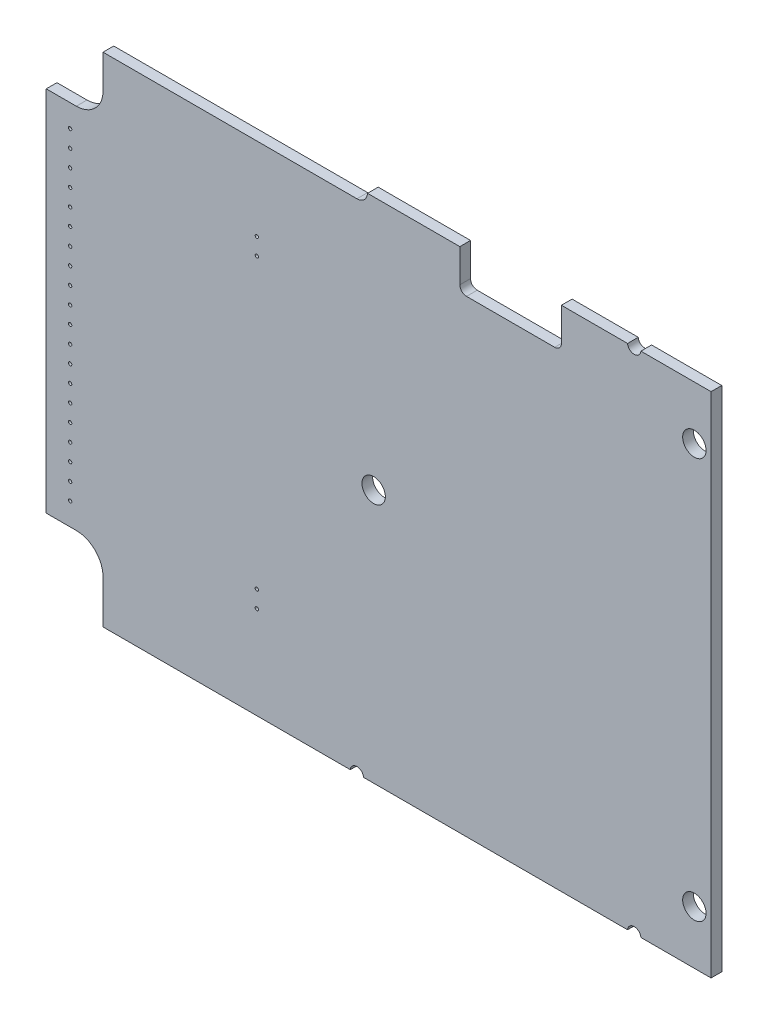
SolidWorks part; units mm, degrees
ref_plane "Płaszczyzna przednia" through (0, 0, 0) normal (0, 0, 1) x (1, 0, 0)
ref_plane "Płaszczyzna górna" through (0, 0, 0) normal (0, 1, 0) x (1, 0, 0)
ref_plane "Płaszczyzna prawa" through (0, 0, 0) normal (1, 0, 0) x (0, 0, -1)
sketch "Sketch1" plane through (0, 0, 0) normal (0, 0, 1) x (1, 0, 0)
  line L0 (293.2004, -11.8195) -> (291.7004, -11.8195) construction
  line L1 (291.7004, -11.8195) -> (291.7004, -12.7695) construction
  line L2 (308.8504, 57.7305) -> (322.0504, 57.7305)
  line L3 (293.2004, -12.7695) -> (293.2004, -11.8195) construction
  line L4 (334.7004, -11.8195) -> (333.2004, -11.8195) construction
  line L5 (333.2004, -11.8195) -> (333.2004, -12.7695) construction
  line L6 (333.2004, 63.6805) -> (333.2004, 63.2305) construction
  line L7 (334.7004, -12.7695) -> (334.7004, -11.8195) construction
  line L8 (376.2004, -11.8195) -> (374.7004, -11.8195) construction
  line L9 (374.7004, -11.8195) -> (374.7004, -12.7695) construction
  line L10 (333.2004, 63.2305) -> (333.2004, 63.1805) construction
  line L11 (376.2004, -12.7695) -> (376.2004, -11.8195) construction
  line L12 (393.4504, -5.0695) -> (393.4504, -6.5695) construction
  line L13 (393.4504, -6.5695) -> (394.4004, -6.5695) construction
  line L14 (333.2004, 63.6805) -> (332.9539, 63.6805) construction
  line L15 (394.4004, -5.0695) -> (393.4504, -5.0695) construction
  line L16 (393.4504, 57.9305) -> (393.4504, 56.4305) construction
  line L17 (393.4504, 56.4305) -> (394.4004, 56.4305) construction
  line L18 (333.2004, 63.6805) -> (323.0504, 63.6805) construction
  line L19 (394.4004, 57.9305) -> (393.4504, 57.9305) construction
  line L20 (333.2004, 63.1805) -> (334.7004, 63.1805) construction
  line L21 (334.7004, 63.1805) -> (334.7004, 64.1305) construction
  line L22 (333.2004, 64.425) -> (333.2004, 63.6805) construction
  line L23 (333.2004, 64.1305) -> (333.2004, 63.1805) construction
  line L24 (374.7004, 63.1805) -> (376.2004, 63.1805) construction
  line L25 (376.2004, 63.1805) -> (376.2004, 64.1305) construction
  line L26 (334.7004, 63.6805) -> (334.7004, 64.425) construction
  line L27 (374.7004, 64.1305) -> (374.7004, 63.1805) construction
  line L28 (291.7004, 63.1805) -> (293.2004, 63.1805) construction
  line L29 (293.2004, 63.1805) -> (293.2004, 64.1305) construction
  line L30 (291.4539, 63.6805) -> (254.4504, 63.6805) construction
  line L31 (291.7004, 64.1305) -> (291.7004, 63.1805) construction
  line L32 (376.2004, -13.3195) -> (390.9504, -13.3195) construction
  line L33 (394.9504, -9.3195) -> (394.9504, -6.5695) construction
  line L34 (394.9504, -5.0695) -> (394.9504, 56.4305) construction
  line L35 (394.9504, 57.9305) -> (394.9504, 60.6805) construction
  line L36 (390.9504, 64.6805) -> (376.2004, 64.6805) construction
  line L37 (374.7004, 64.6805) -> (334.7004, 64.6805) construction
  line L38 (307.8504, 64.6805) -> (307.8504, 65.8305) construction
  line L39 (323.0504, 64.6805) -> (323.0504, 65.8305) construction
  line L40 (333.2004, 64.6805) -> (323.0504, 64.6805) construction
  line L41 (307.8504, 64.6805) -> (293.2004, 64.6805) construction
  line L42 (291.7004, 64.6805) -> (246.9504, 64.6805) construction
  line L43 (246.9504, -8.4262) -> (246.9504, 59.7871) construction
  line L44 (334.7004, -13.3195) -> (374.7004, -13.3195) construction
  line L45 (293.2004, -13.3195) -> (333.2004, -13.3195) construction
  line L46 (246.9504, -13.3195) -> (291.7004, -13.3195) construction
  line L47 (293.2004, -11.8195) -> (291.7004, -11.8195) construction
  line L48 (291.7004, -11.8195) -> (291.7004, -13.3195) construction
  line L50 (293.2004, -13.3195) -> (293.2004, -11.8195) construction
  line L51 (334.7004, -11.8195) -> (333.2004, -11.8195) construction
  line L52 (333.2004, -11.8195) -> (333.2004, -13.3195) construction
  line L54 (334.7004, -13.3195) -> (334.7004, -11.8195) construction
  line L55 (376.2004, -11.8195) -> (374.7004, -11.8195) construction
  line L56 (374.7004, -11.8195) -> (374.7004, -13.3195) construction
  line L58 (376.2004, -13.3195) -> (376.2004, -13.0641) construction
  line L59 (393.4504, -5.0695) -> (393.4504, -6.5695) construction
  line L60 (393.4504, -6.5695) -> (394.9504, -6.5695) construction
  line L62 (394.9504, -5.0695) -> (393.4504, -5.0695) construction
  line L63 (393.4504, 57.9305) -> (393.4504, 56.4305) construction
  line L64 (393.4504, 56.4305) -> (394.6949, 56.4305) construction
  line L66 (394.9504, 57.9305) -> (393.4504, 57.9305) construction
  line L67 (333.2004, 63.1805) -> (334.7004, 63.1805) construction
  line L68 (334.7004, 63.1805) -> (334.7004, 63.6805) construction
  line L70 (333.2004, 64.6805) -> (333.2004, 64.425) construction
  line L71 (374.7004, 63.1805) -> (376.2004, 63.1805) construction
  line L72 (376.2004, 63.1805) -> (376.2004, 63.6805) construction
  line L74 (374.7004, 64.425) -> (374.7004, 63.1805) construction
  line L75 (291.7004, 63.1805) -> (293.2004, 63.1805) construction
  line L76 (293.2004, 63.1805) -> (293.2004, 64.6805) construction
  line L78 (291.7004, 64.425) -> (291.7004, 63.6805) construction
  line L79 (376.2004, -13.3195) -> (390.9504, -13.3195) construction
  line L80 (394.9504, -9.3195) -> (394.9504, -6.5695) construction
  line L81 (394.9504, -5.0695) -> (394.9504, 56.4305) construction
  line L82 (394.9504, 57.9305) -> (394.9504, 60.6805) construction
  line L83 (390.9504, 64.6805) -> (376.2004, 64.6805) construction
  line L84 (374.7004, 64.6805) -> (334.7004, 64.6805) construction
  line L85 (307.8504, 64.6805) -> (307.8504, 65.8305) construction
  line L86 (323.0504, 58.7305) -> (323.0504, 63.6805)
  line L87 (333.2004, 64.6805) -> (323.0504, 64.6805) construction
  line L88 (307.8504, 64.6805) -> (293.2004, 64.6805) construction
  line L89 (291.7004, 64.6805) -> (246.9504, 64.6805) construction
  line L90 (246.9504, -13.3195) -> (246.9504, -3.883) construction
  line L91 (334.7004, -13.3195) -> (374.7004, -13.3195) construction
  line L92 (293.2004, -13.3195) -> (333.2004, -13.3195) construction
  line L93 (246.9504, -13.3195) -> (291.7004, -13.3195) construction
  line L94 (247.9504, -12.3195) -> (247.9504, -8.942) construction
  line L95 (254.4504, -12.3195) -> (291.4539, -12.3195)
  line L96 (293.4469, -12.3195) -> (332.9539, -12.3195)
  line L97 (334.9469, -12.3195) -> (374.4539, -12.3195)
  line L98 (376.4469, -12.3195) -> (390.9504, -12.3195)
  line L99 (393.9504, -9.3195) -> (393.9504, -6.8161)
  line L100 (393.9504, -4.823) -> (393.9504, 56.4305)
  line L101 (393.9504, 58.177) -> (393.9504, 60.6805)
  line L102 (317.8504, 58.7305) -> (317.8504, 63.2305)
  line L103 (317.8504, 63.2305) -> (307.8504, 63.2305)
  line L104 (307.8504, 63.2305) -> (307.8504, 58.7305)
  line L105 (307.8504, 58.7305) -> (311.3504, 58.7305)
  line L106 (311.3504, 58.7305) -> (311.3504, 62.7305)
  line L107 (311.3504, 62.7305) -> (314.3504, 62.7305)
  line L108 (314.3504, 62.7305) -> (314.3504, 58.7305)
  line L109 (314.3504, 58.7305) -> (317.8504, 58.7305)
  line L112 (307.8504, 63.6805) -> (307.8504, 58.7305)
  line L113 (307.8504, 58.7305) -> (311.3504, 58.7305) construction
  line L114 (311.3504, 58.7305) -> (311.3504, 62.7305) construction
  line L115 (311.3504, 62.7305) -> (314.3504, 62.7305) construction
  line L116 (314.3504, 62.7305) -> (314.3504, 58.7305) construction
  line L117 (314.3504, 58.7305) -> (323.0504, 58.7305) construction
  line L118 (390.9504, 63.6805) -> (376.4469, 63.6805)
  line L119 (374.4539, 63.6805) -> (334.9469, 63.6805)
  line L120 (307.8504, 63.6805) -> (294.0313, 63.6805)
  line L121 (332.9539, 63.6805) -> (323.0504, 63.6805)
  line L122 (307.8504, 64.6805) -> (307.8504, 63.6805) construction
  line L123 (323.0504, 64.6805) -> (323.0504, 65.8305) construction
  line L124 (323.0504, 63.6805) -> (323.0504, 64.6805) construction
  line L125 (334.7004, 64.425) -> (334.7004, 64.6805) construction
  line L126 (334.9469, 63.6805) -> (334.7004, 63.6805) construction
  line L127 (374.7004, 63.6805) -> (334.7004, 63.6805) construction
  line L128 (291.7004, 63.6805) -> (291.4539, 63.6805) construction
  line L129 (291.7004, 63.6805) -> (247.9504, 63.6805) construction
  line L130 (291.7004, 64.6805) -> (291.7004, 64.425) construction
  line L131 (293.4469, 63.6805) -> (293.2004, 63.6805) construction
  line L132 (307.8504, 63.6805) -> (293.2004, 63.6805) construction
  line L133 (374.7004, 63.6805) -> (374.4539, 63.6805) construction
  line L134 (374.7004, 64.6805) -> (374.7004, 64.425) construction
  line L135 (376.2004, 63.6805) -> (376.2004, 64.425) construction
  line L136 (376.2004, 64.425) -> (376.2004, 64.6805) construction
  line L137 (376.4469, 63.6805) -> (376.2004, 63.6805) construction
  line L138 (390.9504, 63.6805) -> (376.2004, 63.6805) construction
  line L139 (394.6949, 56.4305) -> (394.9504, 56.4305) construction
  line L140 (393.9504, 57.9305) -> (393.9504, 58.177) construction
  line L141 (393.9504, 57.9305) -> (393.9504, 60.6805) construction
  line L142 (393.9504, -5.0695) -> (393.9504, -4.823) construction
  line L143 (393.9504, -5.0695) -> (393.9504, 56.4305) construction
  line L144 (393.9504, -6.8161) -> (393.9504, -6.5695) construction
  line L145 (393.9504, -9.3195) -> (393.9504, -6.5695) construction
  line L146 (376.2004, -13.0641) -> (376.2004, -12.3195) construction
  line L147 (376.2004, -12.3195) -> (376.2004, -11.8195) construction
  line L148 (376.2004, -12.3195) -> (376.4469, -12.3195) construction
  line L149 (376.2004, -12.3195) -> (390.9504, -12.3195) construction
  line L150 (293.2004, -12.3195) -> (293.4469, -12.3195) construction
  line L151 (332.9539, -12.3195) -> (333.2004, -12.3195) construction
  line L152 (293.2004, -12.3195) -> (333.2004, -12.3195) construction
  line L153 (334.7004, -12.3195) -> (334.9469, -12.3195) construction
  line L154 (334.7004, -12.3195) -> (374.7004, -12.3195) construction
  line L155 (254.4504, 57.1805) -> (254.4504, 62.1805)
  line L156 (291.4539, -12.3195) -> (291.7004, -12.3195) construction
  line L157 (247.9504, -12.3195) -> (291.7004, -12.3195) construction
  line L158 (250.4504, 53.1805) -> (245.9504, 53.1805)
  line L159 (254.4504, -5.8195) -> (254.4504, -12.3195)
  line L160 (250.4504, -1.8195) -> (245.9504, -1.8195)
  line L161 (247.9504, -1.8195) -> (247.9504, 53.1805) construction
  line L162 (247.9504, -4.1612) -> (247.9504, -2.697) construction
  line L163 (247.9504, -2.697) -> (247.9504, -1.8195) construction
  line L164 (247.9504, -12.3195) -> (247.9504, 63.6805) construction
  line L165 (247.9504, -8.942) -> (247.9504, -7.4778) construction
  line L166 (247.9504, -7.4778) -> (247.9504, -4.1612) construction
  line L167 (247.9504, -12.3195) -> (254.4504, -12.3195) construction
  line L168 (247.9504, 60.303) -> (247.9504, 63.6805) construction
  line L169 (254.4504, 63.6805) -> (247.9504, 63.6805) construction
  line L170 (247.9504, 58.8388) -> (247.9504, 60.303) construction
  line L171 (246.9504, 59.117) -> (246.9504, 64.6805) construction
  line L172 (246.9504, -13.3195) -> (246.9504, 64.6805) construction
  line L173 (246.9504, 55.244) -> (246.9504, 59.117) construction
  line L174 (247.9504, 55.5222) -> (247.9504, 58.8388) construction
  line L175 (246.9504, -3.883) -> (246.9504, 55.244) construction
  line L176 (247.9504, 54.058) -> (247.9504, 55.5222) construction
  line L177 (247.9504, 53.1805) -> (247.9504, 54.058) construction
  line L178 (249.5254, 49.8105) -> (277.4654, 49.8105) construction
  line L179 (249.5254, 49.8105) -> (249.5254, 47.2705) construction
  line L180 (374.4539, -12.3195) -> (374.7004, -12.3195) construction
  line L181 (245.4504, -8.8119) -> (245.4504, 59.8484) construction
  line L182 (245.4504, -8.8119) -> (245.4504, 59.8484) construction
  line L183 (245.9504, -1.8195) -> (245.9504, 53.1805)
  line L184 (245.9504, -8.8119) -> (245.9504, -1.8195) construction
  line L185 (245.9504, 53.1805) -> (245.9504, 59.8484) construction
  line L186 (245.9504, -8.8119) -> (245.9504, 59.8484) construction
  line L187 (292.4504, 62.7636) -> (254.4504, 62.7636) construction
  line L188 (254.4504, 62.7636) -> (254.4504, 63.6805) construction
  line L189 (291.7004, 63.6805) -> (291.7004, 63.2305) construction
  line L190 (291.7004, 63.2305) -> (291.7004, 63.1805) construction
  line L195 (292.4504, 62.1805) -> (254.4504, 62.1805)
  line L196 (294.0313, 63.6805) -> (293.4469, 63.6805) construction
  line L197 (254.4504, 62.1805) -> (254.4504, 62.7636) construction
  circle A0 centre (250.4504, -5.8195) radius 1.2 construction
  arc A1 (390.9504, -13.3195) -> (394.9504, -9.3195) centre (390.9504, -9.3195) ccw construction
  arc A2 (394.9504, 60.6805) -> (390.9504, 64.6805) centre (390.9504, 60.6805) ccw construction
  circle A3 centre (249.5254, 49.8105) radius 0.25 construction
  circle A4 centre (250.4504, 57.1805) radius 3 construction
  circle A5 centre (250.4504, 57.1805) radius 1.2 construction
  circle A6 centre (250.4504, -5.8195) radius 3 construction
  circle A7 centre (342.9504, -4.3195) radius 2.5 construction
  circle A8 centre (342.9504, -4.3195) radius 1 construction
  circle A9 centre (375.4504, -5.8195) radius 3 construction
  circle A10 centre (375.4504, -5.8195) radius 1.2 construction
  circle A11 centre (375.4504, 57.1805) radius 3 construction
  circle A12 centre (375.4504, 57.1805) radius 1.2 construction
  circle A13 centre (342.9504, 55.6805) radius 2.5 construction
  circle A14 centre (342.9504, 55.6805) radius 1 construction
  circle A15 centre (294.9504, 25.6805) radius 2.5 construction
  circle A16 centre (294.9504, 25.6805) radius 1 construction
  circle A17 centre (250.4504, -5.8195) radius 1.2 construction
  arc A18 (390.9504, -13.3195) -> (394.9504, -9.3195) centre (390.9504, -9.3195) ccw construction
  arc A19 (394.9504, 60.6805) -> (390.9504, 64.6805) centre (390.9504, 60.6805) ccw construction
  circle A20 centre (249.5254, 49.8105) radius 0.25 construction
  arc A21 (247.9504, 55.5222) -> (247.9504, 58.8388) centre (250.4504, 57.1805) ccw construction
  circle A22 centre (250.4504, 57.1805) radius 1.2 construction
  circle A23 centre (250.4504, -5.8195) radius 3 construction
  circle A24 centre (342.9504, -4.3195) radius 2.5 construction
  circle A25 centre (342.9504, -4.3195) radius 1 construction
  circle A26 centre (375.4504, -5.8195) radius 3 construction
  circle A27 centre (375.4504, -5.8195) radius 1.2 construction
  circle A28 centre (375.4504, 57.1805) radius 3 construction
  circle A29 centre (375.4504, 57.1805) radius 1.2 construction
  circle A30 centre (342.9504, 55.6805) radius 2.5 construction
  circle A31 centre (342.9504, 55.6805) radius 1 construction
  circle A32 centre (294.9504, 25.6805) radius 2.5 construction
  circle A33 centre (294.9504, 25.6805) radius 1 construction
  circle A34 centre (294.9504, 25.6805) radius 1.75
  circle A35 centre (342.9504, 55.6805) radius 1.75
  circle A36 centre (342.9504, -4.3195) radius 1.75
  arc A37 (250.4504, 53.1805) -> (254.4504, 57.1805) centre (250.4504, 57.1805) ccw
  arc A38 (254.4504, -5.8195) -> (250.4504, -1.8195) centre (250.4504, -5.8195) ccw
  circle A39 centre (375.4504, -5.8195) radius 4
  circle A40 centre (375.4504, 57.1805) radius 4
  arc A41 (390.9504, -12.3195) -> (393.9504, -9.3195) centre (390.9504, -9.3195) ccw
  arc A42 (393.9504, 60.6805) -> (390.9504, 63.6805) centre (390.9504, 60.6805) ccw
  arc A43 (307.8504, 58.7305) -> (308.8504, 57.7305) centre (308.8504, 58.7305) ccw
  arc A44 (322.0504, 57.7305) -> (323.0504, 58.7305) centre (322.0504, 58.7305) ccw
  circle A46 centre (333.2004, 63.1805) radius 0.05 construction
  circle A47 centre (334.7004, 63.1805) radius 0.05 construction
  arc A48 (332.9539, 63.6805) -> (334.9469, 63.6805) centre (333.9504, 63.7636) ccw
  arc A49 (333.2004, 64.425) -> (332.9539, 63.6805) centre (333.9504, 63.7636) ccw construction
  arc A50 (334.9469, 63.6805) -> (334.7004, 64.425) centre (333.9504, 63.7636) ccw construction
  arc A51 (334.7004, 64.425) -> (333.2004, 64.425) centre (333.9504, 63.7636) ccw construction
  circle A52 centre (291.7004, 63.1805) radius 0.05 construction
  circle A53 centre (293.2004, 63.1805) radius 0.05 construction
  arc A54 (293.2399, 63.1498) -> (293.4469, 63.6805) centre (292.4504, 63.7636) ccw construction
  arc A55 (291.7004, 64.425) -> (291.4539, 63.6805) centre (292.4504, 63.7636) ccw construction
  arc A56 (293.2004, 64.425) -> (291.7004, 64.425) centre (292.4504, 63.7636) ccw construction
  arc A57 (293.4469, 63.6805) -> (293.2004, 64.425) centre (292.4504, 63.7636) ccw construction
  circle A58 centre (374.7004, 63.1805) radius 0.05 construction
  circle A59 centre (376.2004, 63.1805) radius 0.05 construction
  arc A60 (374.4539, 63.6805) -> (376.4469, 63.6805) centre (375.4504, 63.7636) ccw
  arc A61 (374.7004, 64.425) -> (374.4539, 63.6805) centre (375.4504, 63.7636) ccw construction
  arc A62 (376.2004, 64.425) -> (374.7004, 64.425) centre (375.4504, 63.7636) ccw construction
  arc A63 (376.4469, 63.6805) -> (376.2004, 64.425) centre (375.4504, 63.7636) ccw construction
  circle A64 centre (393.4504, 57.9305) radius 0.05 construction
  circle A65 centre (393.4504, 56.4305) radius 0.05 construction
  arc A66 (393.9504, 58.177) -> (393.9504, 56.1839) centre (394.0335, 57.1805) ccw
  arc A67 (394.6949, 56.4305) -> (394.6949, 57.9305) centre (394.0335, 57.1805) ccw construction
  arc A68 (393.9504, 56.1839) -> (394.6949, 56.4305) centre (394.0335, 57.1805) ccw construction
  arc A69 (394.6949, 57.9305) -> (393.9504, 58.177) centre (394.0335, 57.1805) ccw construction
  circle A70 centre (393.4504, -6.5695) radius 0.05 construction
  circle A71 centre (393.4504, -5.0695) radius 0.05 construction
  arc A72 (393.9504, -4.823) -> (393.9504, -6.8161) centre (394.0335, -5.8195) ccw
  arc A73 (394.9504, -5.4204) -> (393.9504, -4.823) centre (394.0335, -5.8195) ccw construction
  arc A74 (393.9504, -6.8161) -> (394.9504, -6.2186) centre (394.0335, -5.8195) ccw construction
  arc A75 (394.9504, -6.2186) -> (394.9504, -5.4204) centre (394.0335, -5.8195) ccw construction
  circle A76 centre (374.7004, -11.8195) radius 0.05 construction
  circle A77 centre (376.2004, -11.8195) radius 0.05 construction
  circle A78 centre (333.2004, -11.8195) radius 0.05 construction
  circle A79 centre (334.7004, -11.8195) radius 0.05 construction
  circle A80 centre (291.7004, -11.8195) radius 0.05 construction
  circle A81 centre (293.2004, -11.8195) radius 0.05 construction
  arc A82 (376.4469, -12.3195) -> (374.4539, -12.3195) centre (375.4504, -12.4026) ccw
  arc A83 (334.9469, -12.3195) -> (332.9539, -12.3195) centre (333.9504, -12.4026) ccw
  arc A84 (293.4469, -12.3195) -> (291.4539, -12.3195) centre (292.4504, -12.4026) ccw
  arc A85 (374.4539, -12.3195) -> (374.7004, -13.0641) centre (375.4504, -12.4026) ccw construction
  arc A86 (374.7004, -13.0641) -> (376.2004, -13.0641) centre (375.4504, -12.4026) ccw construction
  arc A87 (376.2004, -13.0641) -> (376.4469, -12.3195) centre (375.4504, -12.4026) ccw construction
  arc A88 (332.9539, -12.3195) -> (333.2004, -13.0641) centre (333.9504, -12.4026) ccw construction
  arc A89 (333.2004, -13.0641) -> (334.7004, -13.0641) centre (333.9504, -12.4026) ccw construction
  arc A90 (334.7004, -13.0641) -> (334.9469, -12.3195) centre (333.9504, -12.4026) ccw construction
  arc A91 (293.2004, -13.0641) -> (293.4469, -12.3195) centre (292.4504, -12.4026) ccw construction
  arc A92 (291.7004, -13.0641) -> (293.2004, -13.0641) centre (292.4504, -12.4026) ccw construction
  arc A93 (291.4539, -12.3195) -> (291.7004, -13.0641) centre (292.4504, -12.4026) ccw construction
  arc A94 (247.9504, -2.697) -> (246.9504, -3.883) centre (250.4504, -5.8195) ccw construction
  arc A95 (250.4504, -1.8195) -> (247.9504, -2.697) centre (250.4504, -5.8195) ccw construction
  circle A96 centre (250.4504, -5.8195) radius 4 construction
  arc A97 (246.9504, -3.883) -> (246.9504, -7.756) centre (250.4504, -5.8195) ccw construction
  arc A98 (246.9504, -7.756) -> (247.9504, -8.942) centre (250.4504, -5.8195) ccw construction
  arc A99 (247.9504, -8.942) -> (254.4504, -5.8195) centre (250.4504, -5.8195) ccw construction
  arc A100 (247.9504, 60.303) -> (246.9504, 59.117) centre (250.4504, 57.1805) ccw construction
  circle A101 centre (250.4504, 57.1805) radius 4 construction
  arc A102 (246.9504, 59.117) -> (246.9504, 55.244) centre (250.4504, 57.1805) ccw construction
  arc A103 (247.9504, 58.8388) -> (247.9504, 55.5222) centre (250.4504, 57.1805) ccw construction
  circle A104 centre (250.4504, 57.1805) radius 3 construction
  arc A105 (246.9504, 55.244) -> (247.9504, 54.058) centre (250.4504, 57.1805) ccw construction
  arc A106 (247.9504, 54.058) -> (250.4504, 53.1805) centre (250.4504, 57.1805) ccw construction
  arc A107 (254.4504, 57.1805) -> (247.9504, 60.303) centre (250.4504, 57.1805) ccw construction
  circle A108 centre (277.4654, 49.8105) radius 0.25 construction
  circle A109 centre (277.4654, 47.2705) radius 0.25 construction
  arc A110 (291.4539, 63.6805) -> (291.6609, 63.1498) centre (292.4504, 63.7636) ccw construction
  arc A111 (292.4504, 62.7636) -> (293.2399, 63.1498) centre (292.4504, 63.7636) ccw construction
  arc A112 (291.6609, 63.1498) -> (292.4504, 62.7636) centre (292.4504, 63.7636) ccw construction
  arc A113 (292.4504, 62.1805) -> (294.0313, 63.6805) centre (292.4504, 63.7636) ccw
  circle A126 centre (277.4654, 4.0905) radius 0.25 construction
  circle A127 centre (277.4654, 1.5505) radius 0.25 construction
  circle A128 centre (249.5254, 47.2705) radius 0.25 construction
  circle A129 centre (249.5254, 44.7305) radius 0.25 construction
  circle A130 centre (249.5254, 42.1905) radius 0.25 construction
  circle A131 centre (249.5254, 39.6505) radius 0.25 construction
  circle A132 centre (249.5254, 37.1105) radius 0.25 construction
  circle A133 centre (249.5254, 34.5705) radius 0.25 construction
  circle A134 centre (249.5254, 32.0305) radius 0.25 construction
  circle A135 centre (249.5254, 29.4905) radius 0.25 construction
  circle A136 centre (249.5254, 26.9505) radius 0.25 construction
  circle A137 centre (249.5254, 24.4105) radius 0.25 construction
  circle A138 centre (249.5254, 21.8705) radius 0.25 construction
  circle A139 centre (249.5254, 19.3305) radius 0.25 construction
  circle A140 centre (249.5254, 16.7905) radius 0.25 construction
  circle A141 centre (249.5254, 14.2505) radius 0.25 construction
  circle A142 centre (249.5254, 11.7105) radius 0.25 construction
  circle A143 centre (249.5254, 9.1705) radius 0.25 construction
  circle A144 centre (249.5254, 6.6305) radius 0.25 construction
  circle A145 centre (249.5254, 4.0905) radius 0.25 construction
  circle A146 centre (249.5254, 1.5505) radius 0.25 construction
  circle A147 centre (277.4654, 44.7305) radius 0.25 construction
  circle A148 centre (277.4654, 42.1905) radius 0.25 construction
  circle A149 centre (277.4654, 39.6505) radius 0.25 construction
  circle A150 centre (277.4654, 37.1105) radius 0.25 construction
  circle A151 centre (277.4654, 34.5705) radius 0.25 construction
  circle A152 centre (277.4654, 32.0305) radius 0.25 construction
  circle A153 centre (277.4654, 29.4905) radius 0.25 construction
  circle A154 centre (277.4654, 26.9505) radius 0.25 construction
  circle A155 centre (277.4654, 24.4105) radius 0.25 construction
  circle A156 centre (277.4654, 21.8705) radius 0.25 construction
  circle A157 centre (277.4654, 19.3305) radius 0.25 construction
  circle A158 centre (277.4654, 16.7905) radius 0.25 construction
  circle A159 centre (277.4654, 14.2505) radius 0.25 construction
  circle A160 centre (277.4654, 11.7105) radius 0.25 construction
  circle A161 centre (277.4654, 9.1705) radius 0.25 construction
  circle A162 centre (277.4654, 6.6305) radius 0.25 construction
  point P225 (254.4504, -5.8195)
  point P242 (277.4654, 47.2705)
  point P256 (0, 0)
  point P257 (0, 0)
  point P258 (242.0624, -1.7952)
  dimension "D5" = 1
  dimension "D6" = 0.1
  dimension "D7" = 2
  dimension "D13" = 1
  dimension "D16" = 2.54
  dimension "D10" = 27.94
  dimension "D11" = 2.54
  dimension "D14" = 3.575
  dimension "D15" = 13.87
  dimension "D17" = 48.26
  dimension "D1" = 0
  dimension "D2" = 0.75
  dimension "D3" = 1
  dimension "D4" = 1
  dimension "D12" = 0.5
  dimension "D8" = 2
  dimension "D9" = 20
sketch "Sketch3" plane through (0, 0, 0) normal (0, 0, 1) x (1, 0, 0)
  line L9 (254.4504, 57.1805) -> (254.4504, 62.1805) construction
  line L10 (393.9504, -4.823) -> (393.9504, 56.4305) construction
  line L40 (393.9504, -9.3195) -> (393.9504, -6.8161) construction
  line L46 (376.4469, -12.3195) -> (390.9504, -12.3195) construction
  line L47 (334.9469, -12.3195) -> (374.4539, -12.3195) construction
  line L48 (293.4469, -12.3195) -> (332.9539, -12.3195) construction
  line L49 (254.4504, -12.3195) -> (291.4539, -12.3195) construction
  line L50 (254.4504, -5.8195) -> (254.4504, -12.3195) construction
  line L51 (250.4504, -1.8195) -> (245.9504, -1.8195) construction
  line L52 (245.9504, -1.8195) -> (245.9504, 53.1805) construction
  line L53 (250.4504, 53.1805) -> (245.9504, 53.1805) construction
  line L54 (292.4504, 62.1805) -> (254.4504, 62.1805) construction
  line L55 (307.8504, 63.6805) -> (294.0313, 63.6805) construction
  line L56 (307.8504, 63.6805) -> (307.8504, 58.7305) construction
  line L57 (308.8504, 57.7305) -> (322.0504, 57.7305) construction
  line L58 (323.0504, 58.7305) -> (323.0504, 63.6805) construction
  line L59 (332.9539, 63.6805) -> (323.0504, 63.6805) construction
  line L60 (374.4539, 63.6805) -> (334.9469, 63.6805) construction
  line L61 (390.9504, 63.6805) -> (376.4469, 63.6805) construction
  line L62 (393.9504, 58.177) -> (393.9504, 60.6805) construction
  line L63 (254.4504, 57.1805) -> (254.4504, 62.1805)
  line L64 (393.9504, -4.823) -> (393.9504, 56.1839)
  line L65 (393.9504, -9.3195) -> (393.9504, -6.8161)
  line L66 (376.4469, -12.3195) -> (390.9504, -12.3195)
  line L67 (334.9469, -12.3195) -> (374.4539, -12.3195)
  line L68 (293.4469, -12.3195) -> (332.9539, -12.3195)
  line L69 (254.4504, -12.3195) -> (291.4539, -12.3195)
  line L70 (254.4504, -5.8195) -> (254.4504, -12.3195)
  line L71 (250.4504, -1.8195) -> (245.9504, -1.8195)
  line L72 (245.9504, -1.8195) -> (245.9504, 53.1805)
  line L73 (250.4504, 53.1805) -> (245.9504, 53.1805)
  line L74 (292.4504, 62.1805) -> (254.4504, 62.1805)
  line L75 (307.8504, 63.6805) -> (294.0313, 63.6805)
  line L76 (307.8504, 63.6805) -> (307.8504, 58.7305)
  line L77 (308.8504, 57.7305) -> (322.0504, 57.7305)
  line L78 (323.0504, 58.7305) -> (323.0504, 63.6805)
  line L79 (332.9539, 63.6805) -> (323.0504, 63.6805)
  line L80 (374.4539, 63.6805) -> (334.9469, 63.6805)
  line L81 (390.9504, 63.6805) -> (376.4469, 63.6805)
  line L82 (393.9504, 58.177) -> (393.9504, 60.6805)
  line L83 (393.9504, 56.1839) -> (393.9504, 56.4305) construction
  arc A30 (393.9504, -4.823) -> (393.9504, -6.8161) centre (394.0335, -5.8195) ccw construction
  arc A31 (390.9504, -12.3195) -> (393.9504, -9.3195) centre (390.9504, -9.3195) ccw construction
  arc A32 (376.4469, -12.3195) -> (374.4539, -12.3195) centre (375.4504, -12.4026) ccw construction
  arc A33 (334.9469, -12.3195) -> (332.9539, -12.3195) centre (333.9504, -12.4026) ccw construction
  arc A34 (293.4469, -12.3195) -> (291.4539, -12.3195) centre (292.4504, -12.4026) ccw construction
  arc A35 (254.4504, -5.8195) -> (250.4504, -1.8195) centre (250.4504, -5.8195) ccw construction
  arc A36 (250.4504, 53.1805) -> (254.4504, 57.1805) centre (250.4504, 57.1805) ccw construction
  arc A37 (292.4504, 62.1805) -> (294.0313, 63.6805) centre (292.4504, 63.7636) ccw construction
  arc A38 (307.8504, 58.7305) -> (308.8504, 57.7305) centre (308.8504, 58.7305) ccw construction
  arc A39 (322.0504, 57.7305) -> (323.0504, 58.7305) centre (322.0504, 58.7305) ccw construction
  arc A40 (332.9539, 63.6805) -> (334.9469, 63.6805) centre (333.9504, 63.7636) ccw construction
  arc A41 (374.4539, 63.6805) -> (376.4469, 63.6805) centre (375.4504, 63.7636) ccw construction
  arc A42 (393.9504, 60.6805) -> (390.9504, 63.6805) centre (390.9504, 60.6805) ccw construction
  arc A43 (393.9504, 58.177) -> (393.9504, 56.1839) centre (394.0335, 57.1805) ccw construction
  arc A44 (393.9504, -4.823) -> (393.9504, -6.8161) centre (394.0335, -5.8195) ccw
  arc A45 (390.9504, -12.3195) -> (393.9504, -9.3195) centre (390.9504, -9.3195) ccw
  arc A46 (376.4469, -12.3195) -> (374.4539, -12.3195) centre (375.4504, -12.4026) ccw
  arc A47 (334.9469, -12.3195) -> (332.9539, -12.3195) centre (333.9504, -12.4026) ccw
  arc A48 (293.4469, -12.3195) -> (291.4539, -12.3195) centre (292.4504, -12.4026) ccw
  arc A49 (254.4504, -5.8195) -> (250.4504, -1.8195) centre (250.4504, -5.8195) ccw
  arc A50 (250.4504, 53.1805) -> (254.4504, 57.1805) centre (250.4504, 57.1805) ccw
  arc A51 (292.4504, 62.1805) -> (294.0313, 63.6805) centre (292.4504, 63.7636) ccw
  arc A52 (307.8504, 58.7305) -> (308.8504, 57.7305) centre (308.8504, 58.7305) ccw
  arc A53 (322.0504, 57.7305) -> (323.0504, 58.7305) centre (322.0504, 58.7305) ccw
  arc A54 (332.9539, 63.6805) -> (334.9469, 63.6805) centre (333.9504, 63.7636) ccw
  arc A55 (374.4539, 63.6805) -> (376.4469, 63.6805) centre (375.4504, 63.7636) ccw
  arc A56 (393.9504, 60.6805) -> (390.9504, 63.6805) centre (390.9504, 60.6805) ccw
  arc A57 (393.9504, 58.177) -> (393.9504, 56.1839) centre (394.0335, 57.1805) ccw
extrude "Boss-Extrude1" add sketch "Sketch3" along normal blind 1.6
sketch "Sketch4" plane through (0, 0, 1.6) normal (0, 0, 1) x (1, 0, 0)
  circle A10 centre (375.4504, -5.8195) radius 4 construction
  circle A11 centre (342.9504, -4.3195) radius 1.75 construction
  circle A12 centre (294.9504, 25.6805) radius 1.75 construction
  circle A13 centre (342.9504, 55.6805) radius 1.75 construction
  circle A14 centre (375.4504, 57.1805) radius 4 construction
  circle A15 centre (375.4504, -5.8195) radius 4
  circle A16 centre (342.9504, -4.3195) radius 1.75
  circle A17 centre (294.9504, 25.6805) radius 1.75
  circle A18 centre (342.9504, 55.6805) radius 1.75
  circle A19 centre (375.4504, 57.1805) radius 4
extrude "Cut-Extrude1" cut sketch "Sketch4" along normal through all and the other way through all
sketch "Sketch5" plane through (0, 0, 1.6) normal (0, 0, 1) x (1, 0, 0)
  line L0 (393.9504, -4.823) -> (393.9504, 56.1839) construction
  line L6 (345.4504, -34.3195) -> (395.4504, -34.3195)
  line L7 (345.4504, -34.3195) -> (345.4504, 85.6805)
  line L8 (345.4504, 85.6805) -> (395.4504, 85.6805)
  line L10 (395.4504, -34.3195) -> (395.4504, 85.6805)
  line L11 (245.4504, -8.8119) -> (245.4504, 59.8484) construction
  point P8 (393.9504, 25.6805)
  point P10 (395.4504, 25.6805)
  dimension "D1" = 100
  dimension "D2" = 50
  dimension "D3" = 120
extrude "Cut-Extrude2" cut sketch "Sketch5" against normal through all
sketch "Sketch6" plane through (0, 0, 1.6) normal (0, 0, 1) x (1, 0, 0)
  circle A0 centre (249.5254, 49.8105) radius 0.25 construction
  circle A1 centre (249.5254, 49.8105) radius 0.25
  circle A2 centre (277.4654, 49.8105) radius 0.25 construction
  circle A3 centre (277.4654, 47.2705) radius 0.25 construction
  circle A4 centre (277.4654, 4.0905) radius 0.25 construction
  circle A5 centre (277.4654, 1.5505) radius 0.25 construction
  circle A6 centre (249.5254, 1.5505) radius 0.25 construction
  circle A7 centre (249.5254, 4.0905) radius 0.25 construction
  circle A8 centre (249.5254, 6.6305) radius 0.25 construction
  circle A9 centre (249.5254, 9.1705) radius 0.25 construction
  circle A10 centre (249.5254, 11.7105) radius 0.25 construction
  circle A11 centre (249.5254, 14.2505) radius 0.25 construction
  circle A12 centre (249.5254, 16.7905) radius 0.25 construction
  circle A13 centre (249.5254, 19.3305) radius 0.25 construction
  circle A14 centre (249.5254, 21.8705) radius 0.25 construction
  circle A15 centre (249.5254, 24.4105) radius 0.25 construction
  circle A16 centre (249.5254, 26.9505) radius 0.25 construction
  circle A17 centre (249.5254, 29.4905) radius 0.25 construction
  circle A18 centre (249.5254, 32.0305) radius 0.25 construction
  circle A19 centre (249.5254, 34.5705) radius 0.25 construction
  circle A20 centre (249.5254, 37.1105) radius 0.25 construction
  circle A21 centre (249.5254, 39.6505) radius 0.25 construction
  circle A22 centre (249.5254, 42.1905) radius 0.25 construction
  circle A23 centre (249.5254, 44.7305) radius 0.25 construction
  circle A24 centre (249.5254, 47.2705) radius 0.25 construction
  circle A25 centre (277.4654, 49.8105) radius 0.25
  circle A26 centre (277.4654, 47.2705) radius 0.25
  circle A27 centre (277.4654, 4.0905) radius 0.25
  circle A28 centre (277.4654, 1.5505) radius 0.25
  circle A29 centre (249.5254, 1.5505) radius 0.25
  circle A30 centre (249.5254, 4.0905) radius 0.25
  circle A31 centre (249.5254, 6.6305) radius 0.25
  circle A32 centre (249.5254, 9.1705) radius 0.25
  circle A33 centre (249.5254, 11.7105) radius 0.25
  circle A34 centre (249.5254, 14.2505) radius 0.25
  circle A35 centre (249.5254, 16.7905) radius 0.25
  circle A36 centre (249.5254, 19.3305) radius 0.25
  circle A37 centre (249.5254, 21.8705) radius 0.25
  circle A38 centre (249.5254, 24.4105) radius 0.25
  circle A39 centre (249.5254, 26.9505) radius 0.25
  circle A40 centre (249.5254, 29.4905) radius 0.25
  circle A41 centre (249.5254, 32.0305) radius 0.25
  circle A42 centre (249.5254, 34.5705) radius 0.25
  circle A43 centre (249.5254, 37.1105) radius 0.25
  circle A44 centre (249.5254, 39.6505) radius 0.25
  circle A45 centre (249.5254, 42.1905) radius 0.25
  circle A46 centre (249.5254, 44.7305) radius 0.25
  circle A47 centre (249.5254, 47.2705) radius 0.25
extrude "Cut-Extrude3" cut sketch "Sketch6" against normal through all
sketch "Sketch7" [suppressed] plane through (0, 0, 0) normal (0, 0, -1) x (-1, 0, 0)
  line L68 (-320.7504, 52.8336) -> (-320.7504, 53.8274) construction
  line L69 (-320.7504, 52.8336) -> (-321.1504, 52.8336) construction
  line L70 (-321.1504, 53.8274) -> (-321.1504, 52.8336) construction
  line L71 (-321.1504, 53.8274) -> (-320.7504, 53.8274) construction
  line L72 (-318.8004, 51.9305) -> (-318.9004, 51.9305) construction
  line L73 (-318.9004, 51.9305) -> (-318.9004, 52.2305) construction
  line L74 (-318.9004, 52.2305) -> (-318.8004, 52.2305) construction
  line L75 (-318.8004, 52.2305) -> (-318.8004, 51.9305) construction
  line L76 (-318.8004, 54.4305) -> (-318.9004, 54.4305) construction
  line L77 (-318.9004, 54.4305) -> (-318.9004, 54.7305) construction
  line L78 (-318.9004, 54.7305) -> (-318.8004, 54.7305) construction
  line L79 (-318.8004, 54.7305) -> (-318.8004, 54.4305) construction
  line L80 (-314.8004, 54.4305) -> (-314.9004, 54.4305) construction
  line L81 (-314.9004, 54.4305) -> (-314.9004, 54.7305) construction
  line L82 (-314.9004, 54.7305) -> (-314.8004, 54.7305) construction
  line L83 (-314.8004, 54.7305) -> (-314.8004, 54.4305) construction
  line L84 (-314.8004, 51.9305) -> (-314.9004, 51.9305) construction
  line L85 (-314.9004, 51.9305) -> (-314.9004, 52.2305) construction
  line L86 (-314.9004, 52.2305) -> (-314.8004, 52.2305) construction
  line L87 (-314.8004, 52.2305) -> (-314.8004, 51.9305) construction
  line L88 (-310.8004, 51.9305) -> (-310.9004, 51.9305) construction
  line L89 (-310.9004, 51.9305) -> (-310.9004, 52.2305) construction
  line L90 (-310.9004, 52.2305) -> (-310.8004, 52.2305) construction
  line L91 (-310.8004, 52.2305) -> (-310.8004, 51.9305) construction
  line L92 (-310.8004, 54.4305) -> (-310.9004, 54.4305) construction
  line L93 (-310.9004, 54.4305) -> (-310.9004, 54.7305) construction
  line L94 (-310.9004, 54.7305) -> (-310.8004, 54.7305) construction
  line L95 (-310.8004, 54.7305) -> (-310.8004, 54.4305) construction
  line L96 (-308.9504, 53.8274) -> (-308.5504, 53.8274) construction
  line L97 (-308.5504, 52.8336) -> (-308.5504, 53.8274) construction
  line L98 (-308.5504, 52.8336) -> (-308.9504, 52.8336) construction
  line L99 (-308.9504, 53.8274) -> (-308.9504, 52.8336) construction
  line L100 (-320.7504, 52.8336) -> (-320.7504, 53.8274) construction
  line L101 (-320.7504, 52.8336) -> (-321.1504, 52.8336) construction
  line L102 (-321.1504, 53.8274) -> (-321.1504, 52.8336) construction
  line L103 (-321.1504, 53.8274) -> (-320.7504, 53.8274) construction
  line L104 (-318.8004, 51.9305) -> (-318.9004, 51.9305) construction
  line L105 (-318.9004, 51.9305) -> (-318.9004, 52.2305) construction
  line L106 (-318.9004, 52.2305) -> (-318.8004, 52.2305) construction
  line L107 (-318.8004, 52.2305) -> (-318.8004, 51.9305) construction
  line L108 (-318.8004, 54.4305) -> (-318.9004, 54.4305) construction
  line L109 (-318.9004, 54.4305) -> (-318.9004, 54.7305) construction
  line L110 (-318.9004, 54.7305) -> (-318.8004, 54.7305) construction
  line L111 (-318.8004, 54.7305) -> (-318.8004, 54.4305) construction
  line L112 (-314.8004, 54.4305) -> (-314.9004, 54.4305) construction
  line L113 (-314.9004, 54.4305) -> (-314.9004, 54.7305) construction
  line L114 (-314.9004, 54.7305) -> (-314.8004, 54.7305) construction
  line L115 (-314.8004, 54.7305) -> (-314.8004, 54.4305) construction
  line L116 (-314.8004, 51.9305) -> (-314.9004, 51.9305) construction
  line L117 (-314.9004, 51.9305) -> (-314.9004, 52.2305) construction
  line L118 (-314.9004, 52.2305) -> (-314.8004, 52.2305) construction
  line L119 (-314.8004, 52.2305) -> (-314.8004, 51.9305) construction
  line L120 (-310.8004, 51.9305) -> (-310.9004, 51.9305) construction
  line L121 (-310.9004, 51.9305) -> (-310.9004, 52.2305) construction
  line L122 (-310.9004, 52.2305) -> (-310.8004, 52.2305) construction
  line L123 (-310.8004, 52.2305) -> (-310.8004, 51.9305) construction
  line L124 (-310.8004, 54.4305) -> (-310.9004, 54.4305) construction
  line L125 (-310.9004, 54.4305) -> (-310.9004, 54.7305) construction
  line L126 (-310.9004, 54.7305) -> (-310.8004, 54.7305) construction
  line L127 (-310.8004, 54.7305) -> (-310.8004, 54.4305) construction
  line L128 (-308.9504, 53.8274) -> (-308.5504, 53.8274) construction
  line L129 (-308.5504, 52.8336) -> (-308.5504, 53.8274) construction
  line L130 (-308.5504, 52.8336) -> (-308.9504, 52.8336) construction
  line L131 (-308.9504, 53.8274) -> (-308.9504, 52.8336) construction
  circle A8 centre (-310.8504, 54.5805) radius 0.4
  circle A9 centre (-308.7504, 53.3305) radius 0.6
  circle A10 centre (-314.8504, 54.5805) radius 0.4
  circle A11 centre (-318.8504, 54.5805) radius 0.4
  circle A12 centre (-314.8504, 52.0805) radius 0.4
  circle A13 centre (-318.8504, 52.0805) radius 0.4
  circle A14 centre (-310.8504, 52.0805) radius 0.4
  circle A15 centre (-320.9504, 53.3305) radius 0.6
  point P7 (-308.7504, 53.8274)
  point P10 (-310.9004, 54.5805)
  point P12 (-310.8504, 54.7305)
  point P20 (-308.5504, 53.3305)
  dimension "D1" = 0.8
  dimension "D2" = 1.2
extrude "Cut-Extrude4" [suppressed] cut sketch "Sketch7" against normal through all
